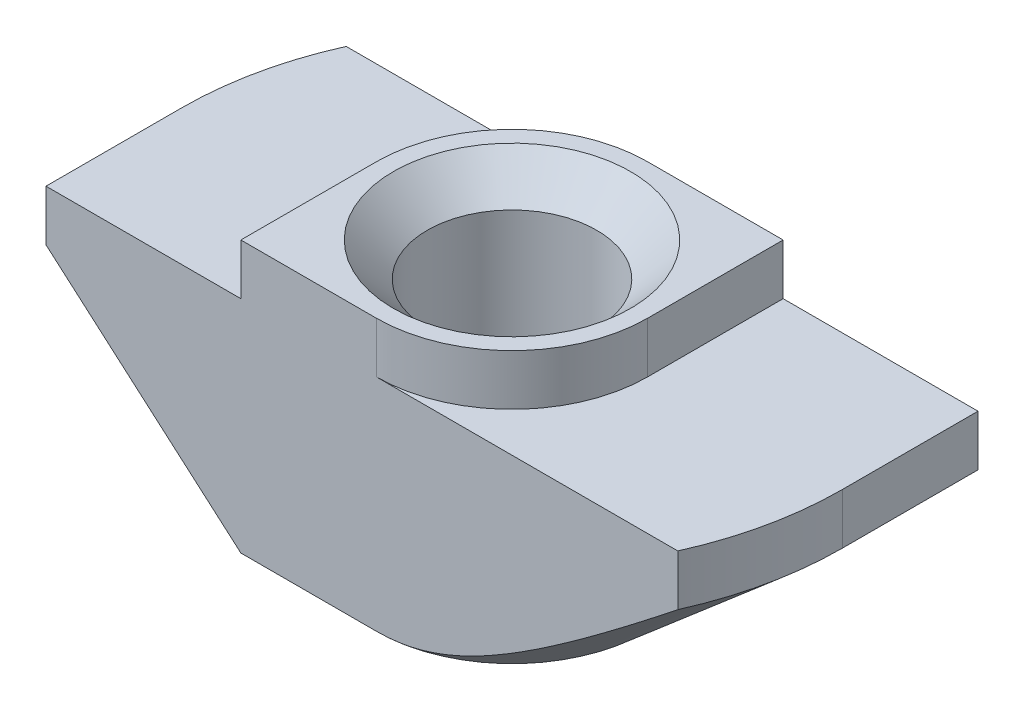
SolidWorks part; units mm, degrees
material "Сталь 20  ГОСТ 1050-2013"
ref_plane "Спереди" through (0, 0, 0) normal (0, 0, 1) x (1, 0, 0)
ref_plane "Сверху" through (0, 0, 0) normal (0, 1, 0) x (1, 0, 0)
ref_plane "Справа" through (0, 0, 0) normal (1, 0, 0) x (0, 0, -1)
sketch "Эскиз1" plane through (0, 0, 0) normal (0, 0, 1) x (1, 0, 0)
  line L0 (4, 0) -> (-4, 0)
  line L1 (-4, 0) -> (-4, -1.5)
  line L2 (-4, -1.5) -> (-9.75, -1.5)
  line L3 (-9.75, -1.5) -> (-9.75, -8)
  line L4 (-9.75, -8) -> (9.75, -8)
  line L5 (0, -8) -> (0, 0) construction
  line L6 (9.75, -1.5) -> (9.75, -8)
  line L7 (4, -1.5) -> (9.75, -1.5)
  line L8 (4, 0) -> (4, -1.5)
  dimension "D1" = 8
  dimension "D2" = 19.5
  dimension "D3" = 8
  dimension "D4" = 1.5
extrude "Бобышка-Вытянуть1" add sketch "Эскиз1" along normal mid plane 8
hole_wizard "Отверстие обработанное метчиком M62" positions "Эскиз2" profile "Эскиз3" tap size "M6" standard "ISO" end condition up to next
sketch "Эскиз2" plane through (0, 0, 0) normal (0, 1, 0) x (1, 0, 0)
  point P0 (0, 0)
sketch "Эскиз3" plane through (0, 0, 0) normal (1, 0, 0) x (0, 0, 1)
  line L0 (0, 0) -> (0, 8)
  line L1 (0, 8) -> (3.5, 8)
  line L2 (2.5, 7) -> (2.5, 1)
  line L3 (2.5, 1) -> (3.5, 0)
  line L5 (3.5, 0) -> (0, 0)
  line L6 (-2.5, 1) -> (-3.5, 0) construction
  line L7 (3.5, 8) -> (2.5, 7)
  line L8 (-3.5, 8) -> (-2.5, 7) construction
  line L11 (0, -6.35) -> (0, 107.95) construction
  dimension "Диаметр проходного сверла" = 5
  dimension "Глубина проходного сверла" = 8
  dimension "Диаметр передней зенковки" = 7
  dimension "Угол передней зенковки" = 90
  dimension "Диаметр задней зенковки" = 7
  dimension "Угол задней зенковки" = 90
cosmetic thread "Отверстие резьбы1" parameters "D2"=6
sketch "Эскиз4" plane through (0, 0, 0) normal (0, 1, 0) x (1, 0, 0)
  line L0 (-4, 4) -> (-4, 0)
  line L1 (-4, -4) -> (-4, 4) construction
  line L2 (4, 4) -> (-4, 4) construction
  line L3 (0, 4) -> (-4, 4)
  line L4 (0, -4) -> (4, -4)
  line L5 (4, -4) -> (-4, -4) construction
  line L6 (4, -4) -> (4, 0)
  line L7 (4, -4) -> (4, 4) construction
  arc A0 (-4, 0) -> (0, 4) centre (0, 0) cw
  arc A1 (4, 0) -> (0, -4) centre (0, 0) cw
extrude "Вырез-Вытянуть1" cut sketch "Эскиз4" against normal up to surface (1.5 mm away) up to face at (-6.875, -1.5, 0)
sketch "Эскиз5" plane through (0, -1.5, 0) normal (0, 1, 0) x (1, 0, 0)
  line L0 (-9.75, 0) -> (-9.75, 4)
  line L1 (-9.75, -4) -> (-9.75, 4) construction
  line L2 (-9.75, 4) -> (-8.8917, 4)
  line L3 (0, 4) -> (-9.75, 4) construction
  line L4 (9.75, 0) -> (9.75, -4)
  line L5 (9.75, -4) -> (9.75, 4) construction
  line L6 (9.75, -4) -> (8.8917, -4)
  line L7 (9.75, -4) -> (0, -4) construction
  arc A0 (-8.8917, 4) -> (-9.75, 0) centre (0, 0) ccw
  arc A2 (9.75, 0) -> (8.8917, -4) centre (0, 0) cw
  point P19 (0, 0)
extrude "Вырез-Вытянуть2" cut sketch "Эскиз5" against normal through all
sketch "Эскиз6" plane through (0, 0, 4) normal (0, 0, 1) x (1, 0, 0)
  line L0 (-9.75, -3) -> (-9.75, -8)
  line L1 (-9.75, -1.5) -> (-9.75, -8) construction
  line L2 (-9.75, -8) -> (-4, -8)
  line L3 (-9.75, -8) -> (8.8917, -8) construction
  line L4 (-4, -8) -> (-9.75, -3)
  line L5 (-4, -1.5) -> (-9.75, -1.5) construction
  line L6 (-4, 0) -> (-4, -1.5) construction
  point P10 (0, 0)
  dimension "D1" = 1.5
sketch "Эскиз7" plane through (0, -8, 0) normal (0, -1, 0) x (1, 0, 0)
  line L0 (0, 9.75) -> (-9.75, 9.75)
  line L1 (-9.75, 9.75) -> (-9.75, 0)
  line L2 (0, -9.75) -> (9.75, -9.75)
  line L3 (9.75, -9.75) -> (9.75, 0)
  arc A0 (-9.75, 0) -> (0, -9.75) centre (0, 0) ccw
  arc A1 (9.75, 0) -> (0, 9.75) centre (0, 0) ccw
sweep "Вырез-По траектории1" cut profiles "Эскиз6" path "Эскиз7"
